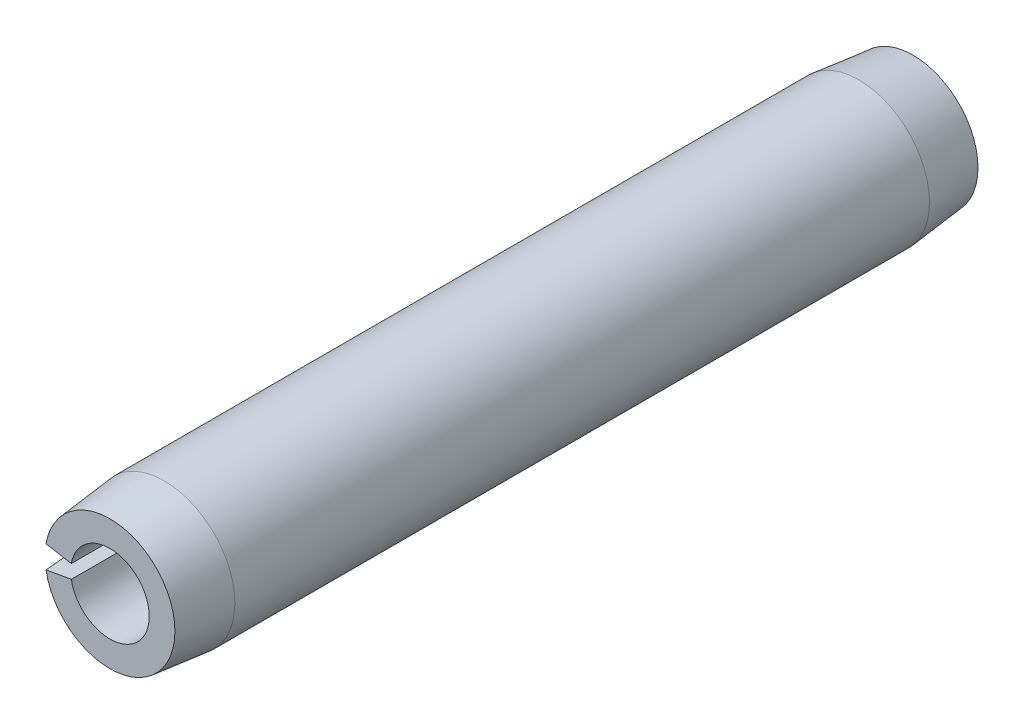
SolidWorks part; units mm, degrees
ref_plane "Front Plane" through (0, 0, 0) normal (0, 0, 1) x (1, 0, 0)
ref_plane "Top Plane" through (0, 0, 0) normal (0, 1, 0) x (1, 0, 0)
ref_plane "Right Plane" through (0, 0, 0) normal (1, 0, 0) x (0, 0, -1)
sketch "Sketch1" plane through (0, 0, 0) normal (0, 0, 1) x (1, 0, 0)
  line L0 (0.6985, 0) -> (1.2573, 0) construction
  line L1 (-1.2382, 0.2183) -> (-0.6879, 0.1213)
  line L2 (-0.6879, -0.1213) -> (-1.2382, -0.2183)
  arc A0 (-1.2382, -0.2183) -> (-1.2382, 0.2183) centre (0, 0) ccw
  arc A1 (-0.6879, -0.1213) -> (-0.6879, 0.1213) centre (0, 0) ccw
  dimension "OD" = 2.5146
  dimension "Wall thickness" = 0.5588
  dimension "D3" = 20
extrude "Extrude1" add sketch "Sketch1" along normal mid plane 14.2875
sketch "Sketch2" plane through (0, 0, 0) normal (1, 0, 0) x (0, 0, -1)
  line L0 (0, -1.2573) -> (0, 1.2573) construction
  line L1 (7.1437, 0) -> (-7.1437, 0) construction
  line L2 (7.1437, -0.6985) -> (7.1437, 0.6985) construction
  line L3 (7.1437, 1.2573) -> (-7.1437, 1.2573) construction
  line L4 (7.1437, 1.2573) -> (7.1437, 1.1557)
  line L5 (7.1437, 1.1557) -> (6.1785, 1.2573)
  line L6 (6.1785, 1.2573) -> (7.1437, 1.2573)
  line L7 (7.1437, -1.2573) -> (7.1437, 1.2573) construction
  line L8 (-6.1785, 1.2573) -> (-7.1437, 1.2573)
  line L9 (-7.1437, 1.1557) -> (-6.1785, 1.2573)
  line L10 (-7.1437, 1.2573) -> (-7.1437, 1.1557)
  line L11 (6.1785, -1.2573) -> (7.1437, -1.2573) construction
  line L12 (7.1437, -1.1557) -> (6.1785, -1.2573) construction
  line L13 (7.1437, -1.2573) -> (7.1437, -1.1557) construction
  dimension "B" = 2.3114
  dimension "Chamfer max" = 0.9652
revolve "Cut-Revolve1" cut sketch "Sketch2" angle 360 about L1
sketch "Sketch3" plane through (0, 0, 0) normal (0, 0, 1) x (1, 0, 0)
  line L0 (0.6985, 0) -> (1.2573, 0) construction
  line L1 (0.6985, 0) -> (1.2573, 0)
  circle A0 centre (0, 0) radius 1.2573
  circle A1 centre (0, 0) radius 0.6985
  arc A2 (-1.2382, -0.2183) -> (-1.2382, 0.2183) centre (0, 0) ccw construction
  arc A3 (-0.6879, -0.1213) -> (-0.6879, 0.1213) centre (0, 0) ccw construction
